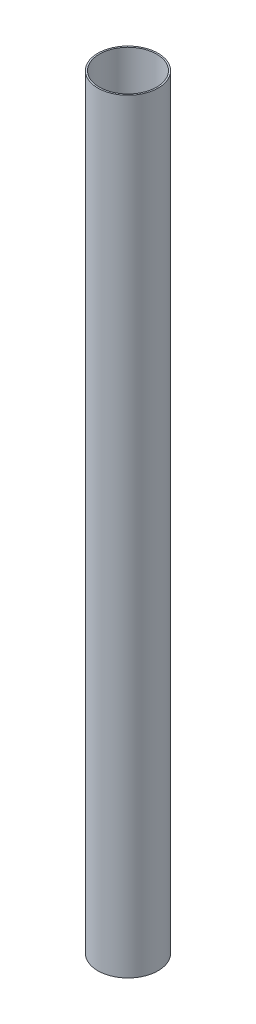
SolidWorks part; units mm, degrees
material "Cardboard"
ref_plane "Frontal Plane" through (0, 0, 0) normal (0, 0, 1) x (1, 0, 0)
ref_plane "Horizontal Plane" through (0, 0, 0) normal (0, 1, 0) x (1, 0, 0)
ref_plane "Profile Plane" through (0, 0, 0) normal (1, 0, 0) x (0, 0, -1)
sketch "Sketch1" plane through (0, 0, 0) normal (0, 1, 0) x (1, 0, 0)
  circle A0 centre (0, 0) radius 10
  circle A1 centre (0, 0) radius 9.5
  dimension "D1" = 19
  dimension "D2" = 20
extrude "Boss-Extrude1" add sketch "Sketch1" along normal blind 253.5
